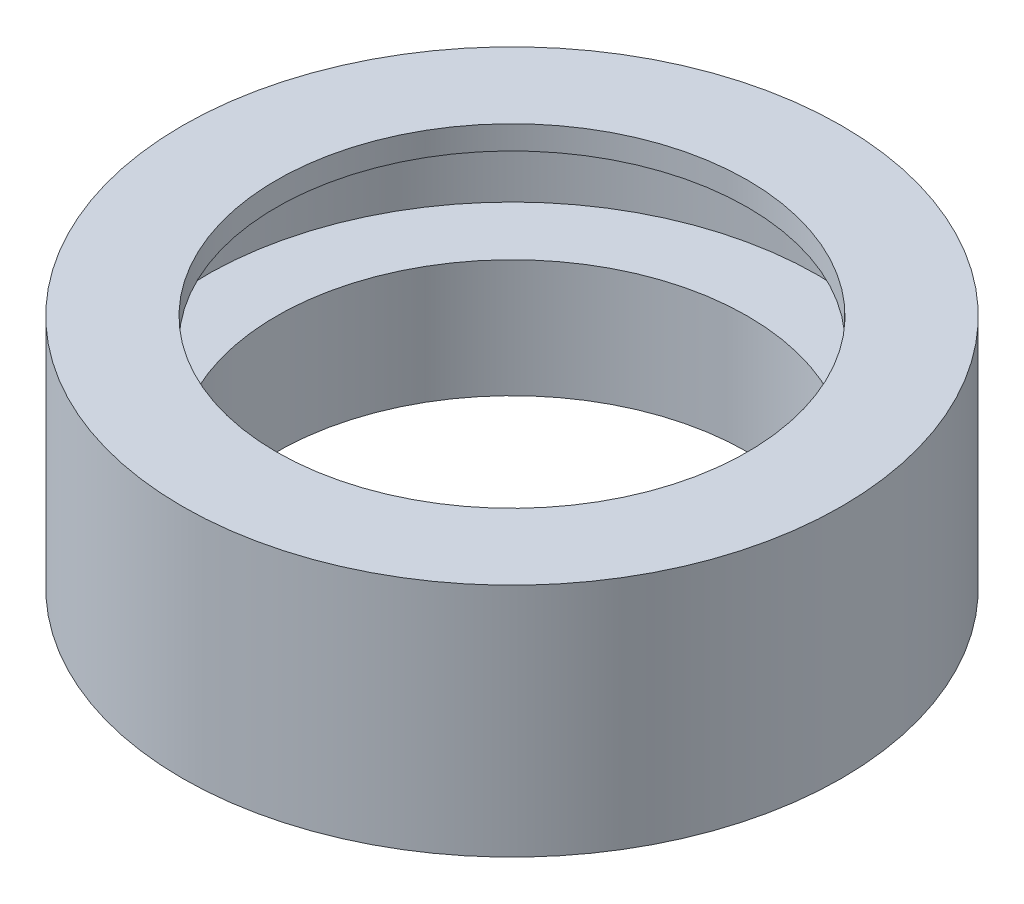
SolidWorks part; units mm, degrees
material "ASTM A36 Steel"
ref_plane "Front Plane" through (0, 0, 0) normal (0, 0, 1) x (1, 0, 0)
ref_plane "Top Plane" through (0, 0, 0) normal (0, 1, 0) x (1, 0, 0)
ref_plane "Right Plane" through (0, 0, 0) normal (1, 0, 0) x (0, 0, -1)
sketch "Sketch2" plane through (0, 0, 0) normal (1, 0, 0) x (0, 0, -1)
  line L0 (0, 0) -> (0, 4.2116)
  line L1 (5, 3.7116) -> (7, 3.7116)
  line L2 (7, 3.7116) -> (7, 13.7116)
  line L3 (7, 13.7116) -> (5, 13.7116)
  line L4 (5, 3.7116) -> (7, 3.7116)
  line L5 (5, 3.7116) -> (5, 6.2116)
  line L6 (5, 6.2116) -> (6.5, 6.2116)
  line L7 (6.5, 6.2116) -> (6.5, 8.2116)
  line L8 (6.5, 8.2116) -> (5, 8.2116)
  line L9 (5, 8.2116) -> (5, 13.7116)
  dimension "D1" = 2
  dimension "D2" = 2.5
  dimension "D3" = 10
  dimension "D4" = 2
  dimension "D5" = 5
revolve "Revolve1" add sketch "Sketch2" angle 360 about L0
sketch "Sketch3" plane through (0, 13.7116, 0) normal (0, 1, 0) x (1, 0, 0)
  circle A0 centre (0, 0) radius 7
extrude "Cut-Extrude1" cut sketch "Sketch3" against normal blind 5
